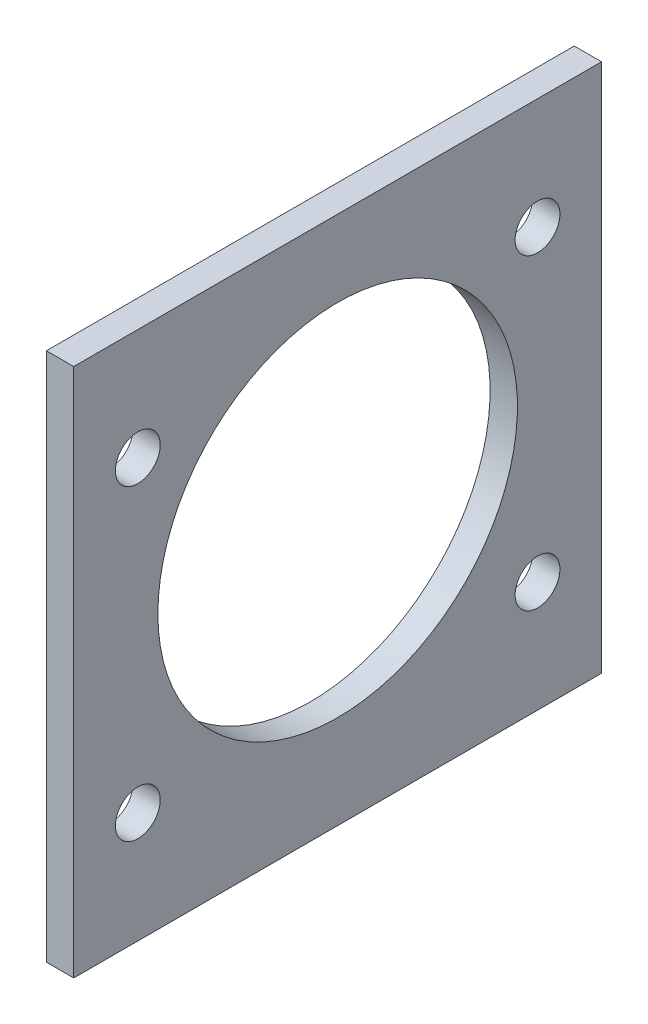
SolidWorks part; units mm, degrees
material "AISI 304"
ref_plane "Front Plane" through (0, 0, 0) normal (0, 0, 1) x (1, 0, 0)
ref_plane "Top Plane" through (0, 0, 0) normal (0, 1, 0) x (1, 0, 0)
ref_plane "Right Plane" through (0, 0, 0) normal (1, 0, 0) x (0, 0, -1)
sketch "Sketch1" plane through (0, 0, 0) normal (1, 0, 0) x (0, 0, -1)
  line L1 (0, 0) -> (61.8, 0)
  line L2 (0, 0) -> (0, 62)
  line L3 (0, 62) -> (61.8, 62)
  line L4 (61.8, 0) -> (61.8, 62)
  dimension "D1" = 61.8
  dimension "D2" = 62
extrude "Boss-Extrude1" add sketch "Sketch1" along normal blind 3.2
sketch "Sketch2" plane through (3.2, 0, 0) normal (1, 0, 0) x (0, 0, -1)
  line L0 (30.9, 62) -> (30.9, 0) construction
  line L1 (61.8, 62) -> (0, 62) construction
  line L2 (0, 0) -> (61.8, 0) construction
  circle A0 centre (30.9, 32) radius 21.05
  point P13 (30.9, 0)
  dimension "D1" = 21.05
  dimension "D2" = 30
extrude "Cut-Extrude1" cut sketch "Sketch2" against normal up to next
sketch "Sketch3" plane through (0, 0, 0) normal (-1, 0, 0) x (0, 0, 1)
  circle A0 centre (-54.3, 49) radius 2.625
  circle A1 centre (-54.3, 13) radius 2.625
  circle A2 centre (-7.5, 49) radius 2.625
  circle A3 centre (-7.5, 13) radius 2.625
extrude "Cut-Extrude2" cut sketch "Sketch3" against normal up to next
